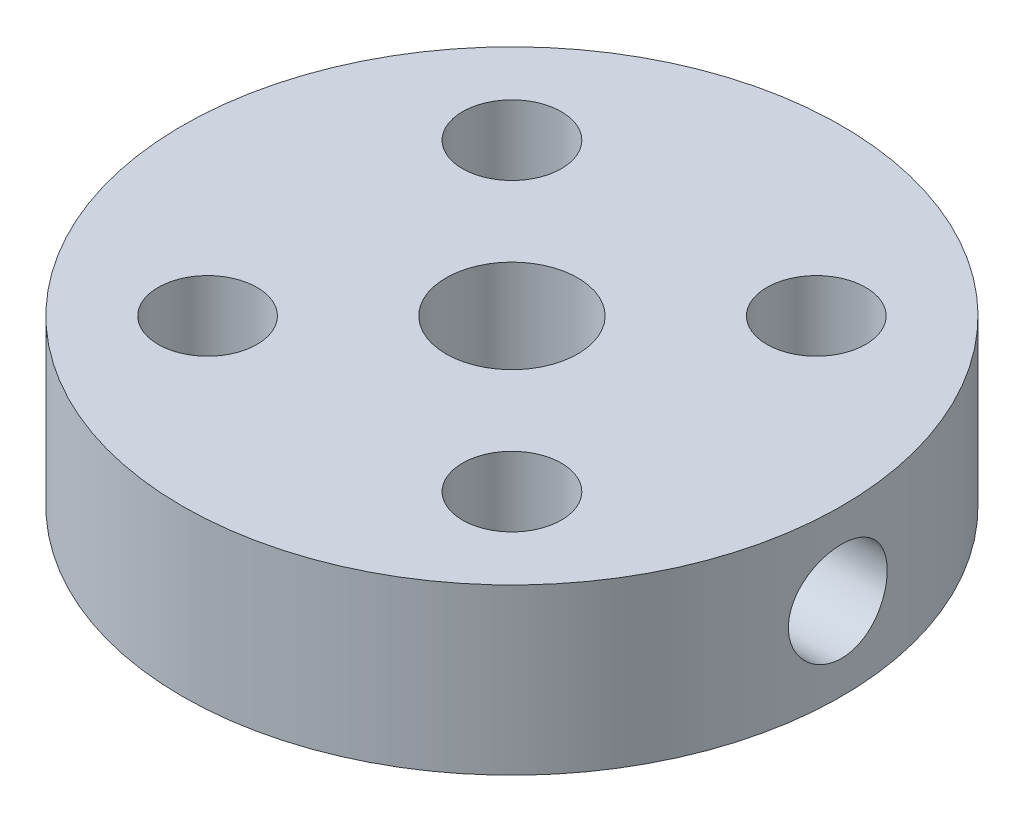
SolidWorks part; units mm, degrees
ref_plane "Спереди" through (0, 0, 0) normal (0, 0, 1) x (1, 0, 0)
ref_plane "Сверху" through (0, 0, 0) normal (0, 1, 0) x (1, 0, 0)
ref_plane "Справа" through (0, 0, 0) normal (1, 0, 0) x (0, 0, -1)
sketch "Эскиз1" plane through (0, 0, 0) normal (0, 1, 0) x (1, 0, 0)
  line L0 (0, 0) -> (0, 10)
  line L1 (0, 0) -> (7.0711, 7.0711)
  circle A0 centre (0, 0) radius 10
  circle A1 centre (0, 0) radius 2
  circle A2 centre (4.6174, 4.6174) radius 1.5
  circle A3 centre (4.6174, -4.6174) radius 1.5
  circle A4 centre (-4.6174, -4.6174) radius 1.5
  circle A5 centre (-4.6174, 4.6174) radius 1.5
  point P17 (0, 0)
  dimension "D1" = 20
  dimension "D3" = 4
  dimension "D5" = 3
  dimension "D2" = 45
  dimension "D4" = 6.53
  dimension "D6" = 4
extrude "Бобышка-Вытянуть1" add sketch "Эскиз1" along normal blind 5 contours A2 L1 A0 L0 A1 | A2 L1 A1 L0 A0 A5 A4 A3
ref_plane "Плоскость1" through (10, 0, 0) normal (1, 0, 0) x (0, 0, -1)
sketch "Эскиз2" plane through (10, 0, 0) normal (1, 0, 0) x (0, 0, -1)
  line L0 (2, 5) -> (-2, 5) construction
  line L1 (10, 0) -> (10, 5) construction
  circle A0 centre (0, 2.5) radius 1.5
  dimension "D2" = 3
  dimension "D1" = 2.5
  dimension "D3" = 10
extrude "Вырез-Вытянуть4" cut sketch "Эскиз2" against normal blind 9
